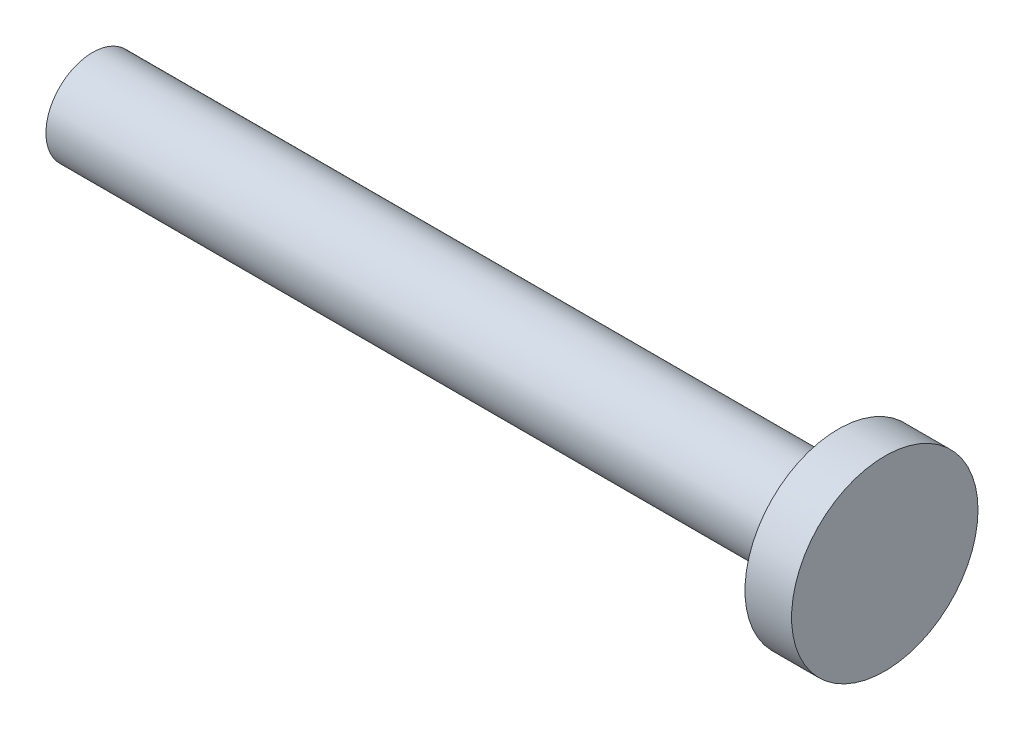
SolidWorks part; units mm, degrees
ref_plane "Front Plane" through (0, 0, 0) normal (0, 0, 1) x (1, 0, 0)
ref_plane "Top Plane" through (0, 0, 0) normal (0, 1, 0) x (1, 0, 0)
ref_plane "Right Plane" through (0, 0, 0) normal (1, 0, 0) x (0, 0, -1)
sketch "Sketch1" plane through (0, 0, 0) normal (1, 0, 0) x (0, 0, -1)
  circle A0 centre (0, 0) radius 6.35
  dimension "D1" = 12.7
extrude "Boss-Extrude1" add sketch "Sketch1" against normal blind 101.6 contours A0
sketch "Sketch2" plane through (0, 0, 0) normal (1, 0, 0) x (0, 0, -1)
  circle A0 centre (0, 0) radius 12.7
  dimension "D1" = 25.4
extrude "Boss-Extrude2" add sketch "Sketch2" along normal blind 6.35
